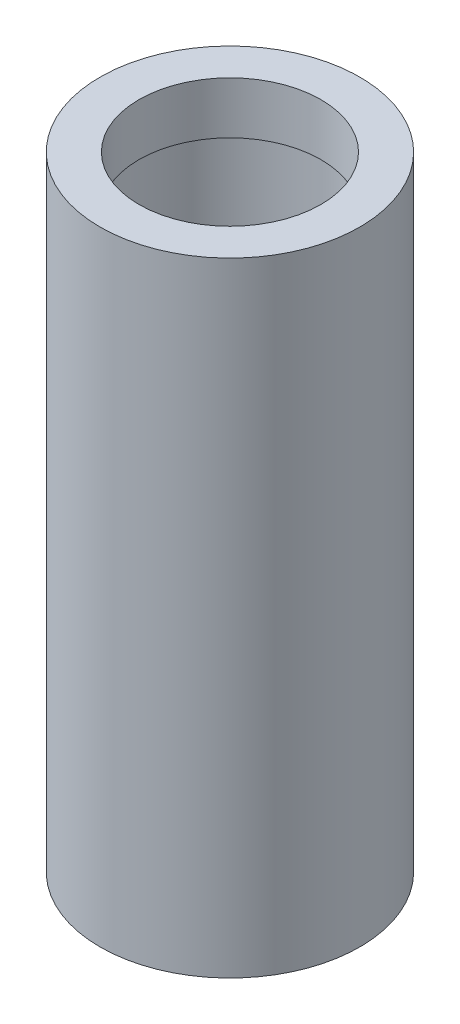
SolidWorks part; units mm, degrees
ref_plane "Front Plane" through (0, 0, 0) normal (0, 0, 1) x (1, 0, 0)
ref_plane "Top Plane" through (0, 0, 0) normal (0, 1, 0) x (1, 0, 0)
ref_plane "Right Plane" through (0, 0, 0) normal (1, 0, 0) x (0, 0, -1)
sketch "Sketch1" plane through (0, 0, 0) normal (0, 1, 0) x (1, 0, 0)
  circle A0 centre (0, 0) radius 25
  circle A1 centre (0, 0) radius 20
extrude "Boss-Extrude1" add sketch "Sketch1" along normal blind 120
sketch "Sketch2" plane through (0, 120, 0) normal (0, 1, 0) x (1, 0, 0)
  circle A0 centre (0, 0) radius 20
  circle A1 centre (0, 0) radius 17.5
extrude "Boss-Extrude2" add sketch "Sketch2" against normal blind 10
sketch "Sketch3" plane through (0, 0, 0) normal (0, -1, 0) x (-1, 0, 0)
  circle A0 centre (0, 0) radius 10
  circle A1 centre (0, 0) radius 20
extrude "Boss-Extrude3" add sketch "Sketch3" against normal blind 10
